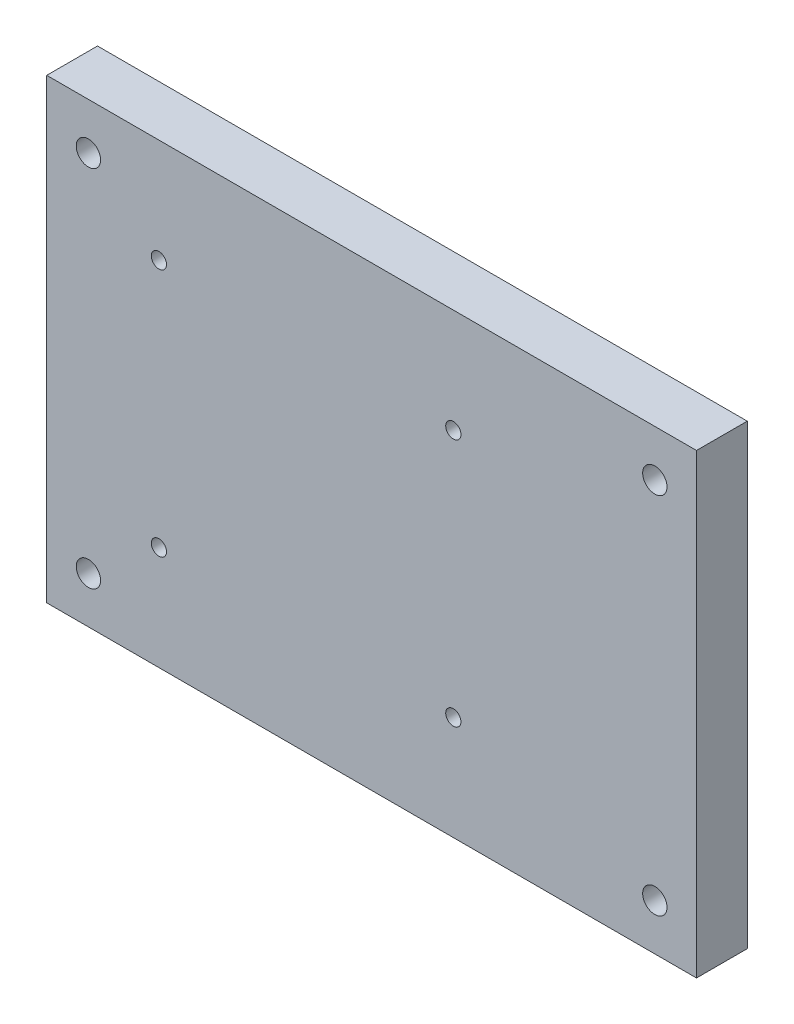
SolidWorks part; units mm, degrees
ref_plane "Front Plane" through (0, 0, 0) normal (0, 0, 1) x (1, 0, 0)
ref_plane "Top Plane" through (0, 0, 0) normal (0, 1, 0) x (1, 0, 0)
ref_plane "Right Plane" through (0, 0, 0) normal (1, 0, 0) x (0, 0, -1)
sketch "Sketch1" plane through (0, 0, 0) normal (0, 0, 1) x (1, 0, 0)
  line L1 (0, 0) -> (-111.58, 0) construction
  line L2 (0, 0) -> (0, 71.73) construction
  line L3 (0, 71.73) -> (-111.58, 71.73) construction
  line L4 (-111.58, 0) -> (-111.58, 71.73) construction
  line L5 (-119.79, 80.875) -> (8.21, 80.875)
  line L6 (-119.79, 80.875) -> (-119.79, -9.125)
  line L7 (-119.79, -9.125) -> (8.21, -9.125)
  line L8 (8.21, 80.875) -> (8.21, -9.125)
  line L9 (-97.6944, 60.375) -> (-39.6944, 60.375) construction
  line L10 (-97.6944, 60.375) -> (-97.6944, 11.375) construction
  line L11 (-97.6944, 11.375) -> (-39.6944, 11.375) construction
  line L12 (-39.6944, 60.375) -> (-39.6944, 11.375) construction
  circle A0 centre (0, 71.73) radius 2.4
  circle A1 centre (-111.58, 0) radius 2.4
  circle A2 centre (0, 0) radius 2.4
  circle A3 centre (-111.58, 71.73) radius 2.4
  circle A4 centre (-97.6944, 60.375) radius 1.5
  circle A5 centre (-39.6944, 60.375) radius 1.5
  circle A6 centre (-39.6944, 11.375) radius 1.5
  circle A7 centre (-97.6944, 11.375) radius 1.5
  dimension "D2" = 4.8
  dimension "D4" = 3
  dimension "D1" = 111.58
  dimension "D3" = 71.73
  dimension "D5" = 58
  dimension "D6" = 49
  dimension "D7" = 20.5
  dimension "D8" = 90
  dimension "D9" = 9.145
  dimension "D10" = 128
  dimension "D11" = 8.21
  dimension "D12" = 22.0956
extrude "Boss-Extrude3" add sketch "Sketch1" along normal blind 10
